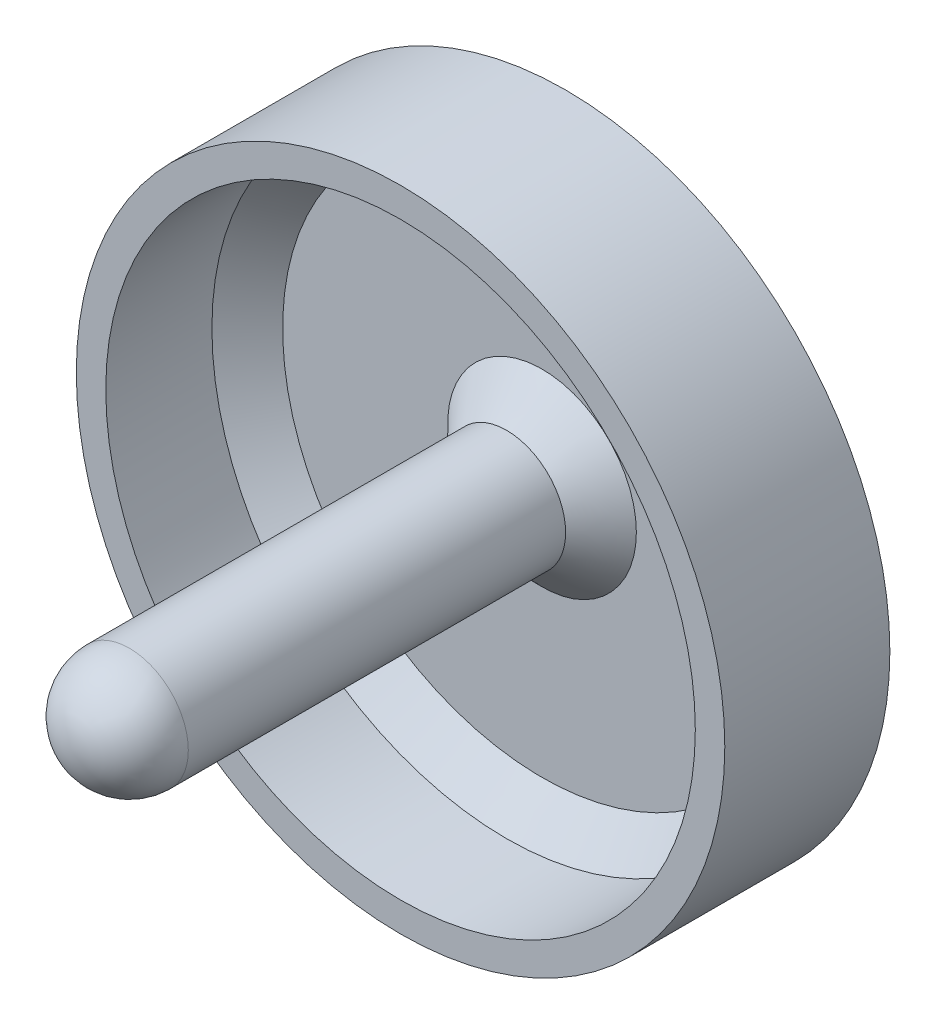
SolidWorks part; units mm, degrees
ref_plane "前视基准面" through (0, 0, 0) normal (0, 0, 1) x (1, 0, 0)
ref_plane "上视基准面" through (0, 0, 0) normal (0, 1, 0) x (1, 0, 0)
ref_plane "右视基准面" through (0, 0, 0) normal (1, 0, 0) x (0, 0, -1)
sketch "草图1" plane through (0, 0, 0) normal (0, 0, 1) x (1, 0, 0)
  circle A0 centre (0, 0) radius 27.5
extrude "凸台-拉伸1" add sketch "草图1" along normal blind 2
sketch "草图2" plane through (0, 0, 2) normal (0, 0, 1) x (1, 0, 0)
  circle A0 centre (0, 0) radius 27.5
  circle A1 centre (0, 0) radius 25
extrude "凸台-拉伸2" add sketch "草图2" along normal blind 12
sketch "草图3" plane through (0, 0, 2) normal (0, 0, 1) x (1, 0, 0)
  circle A0 centre (0, 0) radius 5
extrude "凸台-拉伸3" add sketch "草图3" along normal blind 40
chamfer "倒角2" distance 3 angle 45 1 edges at (25, 0, 2)
chamfer "倒角3" distance 3 angle 45 1 edges at (5, 0, 2)
fillet "圆角3" radius 5 1 edges at (5, 0, 42)
